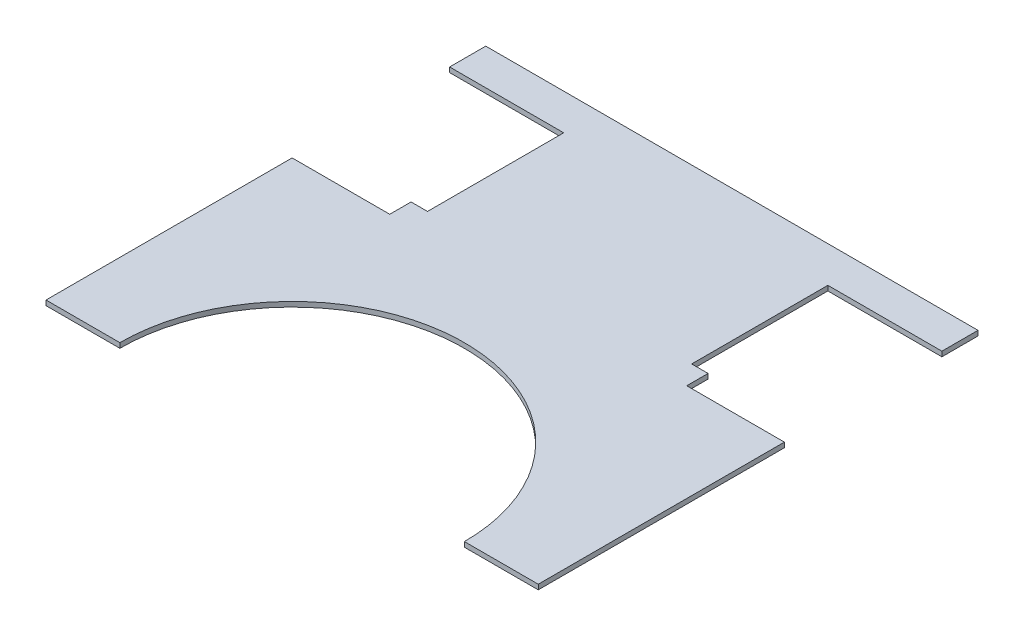
SolidWorks part; units mm, degrees
ref_plane "Face" through (0, 0, 0) normal (0, 0, 1) x (1, 0, 0)
ref_plane "Dessus" through (0, 0, 0) normal (0, 1, 0) x (1, 0, 0)
ref_plane "Droite" through (0, 0, 0) normal (1, 0, 0) x (0, 0, -1)
sketch "Esquisse1" plane through (0, 0, 0) normal (0, 1, 0) x (1, 0, 0)
  line L0 (0, 0) -> (0, -319.3297) construction
  line L1 (150, 0) -> (-150, 0)
  line L2 (-150, 0) -> (-150, -22)
  line L3 (-150, -22) -> (-80.5, -22)
  line L4 (-80.5, -22) -> (-80.5, -105)
  line L5 (-80.5, -105) -> (-90.5, -105)
  line L6 (-90.5, -105) -> (-90.5, -118)
  line L7 (-90.5, -118) -> (-150, -118)
  line L8 (-150, -118) -> (-150, -268)
  line L9 (-150, -268) -> (-105, -268)
  line L10 (150, -268) -> (105, -268)
  line L11 (150, -118) -> (150, -268)
  line L12 (90.5, -118) -> (150, -118)
  line L13 (90.5, -105) -> (90.5, -118)
  line L14 (80.5, -105) -> (90.5, -105)
  line L15 (80.5, -22) -> (80.5, -105)
  line L16 (150, -22) -> (80.5, -22)
  line L17 (150, 0) -> (150, -22)
  line L18 (-105, -268) -> (0, -268) construction
  arc A0 (-105, -268) -> (105, -268) centre (0, -268) cw
  dimension "D7" = 105
  dimension "D1" = 150
  dimension "D2" = 22
  dimension "D3" = 80.5
  dimension "D4" = 83
  dimension "D5" = 10
  dimension "D6" = 13
  dimension "D8" = 150
extrude "Extrusion1" add sketch "Esquisse1" along normal blind 3
